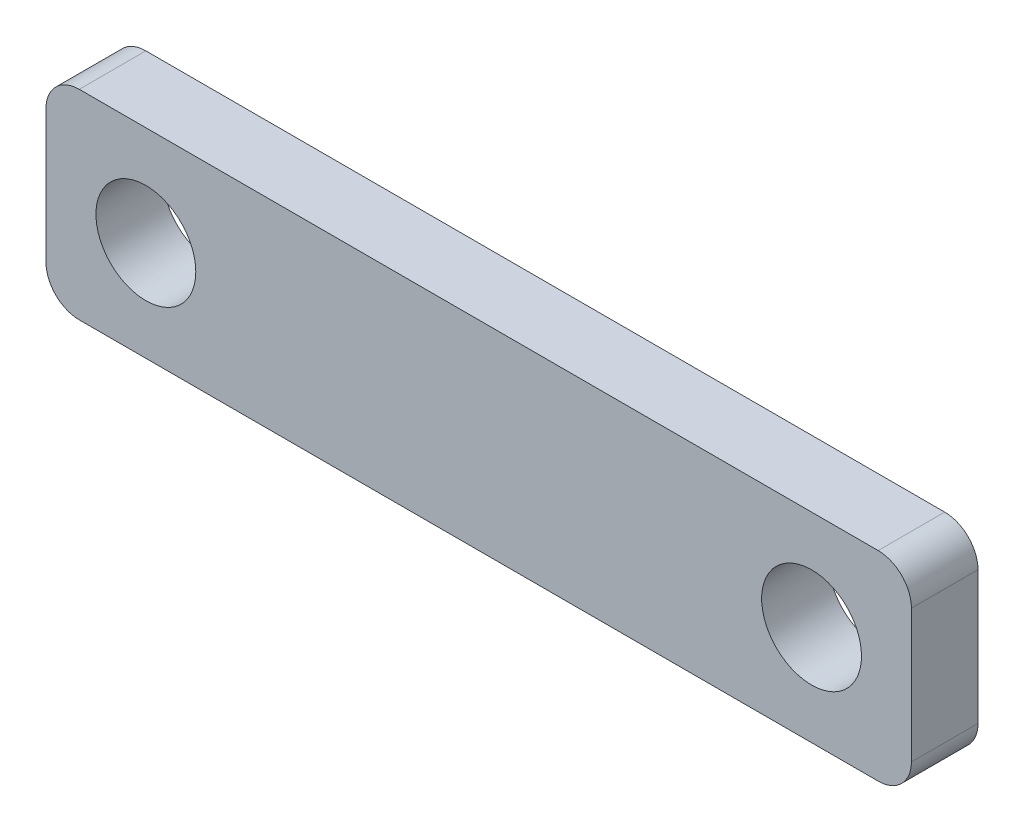
SolidWorks part; units mm, degrees
ref_plane "Plan de face" through (0, 0, 0) normal (0, 0, 1) x (1, 0, 0)
ref_plane "Plan de dessus" through (0, 0, 0) normal (0, 1, 0) x (1, 0, 0)
ref_plane "Plan de droite" through (0, 0, 0) normal (1, 0, 0) x (0, 0, -1)
sketch "Esquisse1" plane through (0, 0, 0) normal (0, 0, 1) x (1, 0, 0)
  line L1 (-13, -3) -> (13, -3)
  line L2 (-13, -3) -> (-13, 3)
  line L3 (-13, 3) -> (13, 3)
  line L4 (13, -3) -> (13, 3)
  line L5 (-13, -3) -> (13, 3) construction
  line L6 (-13, 3) -> (13, -3) construction
  circle A0 centre (10, 0) radius 1.5
  circle A1 centre (-10, 0) radius 1.5
  point P0 (0, 0)
  dimension "D3" = 3
  dimension "D1" = 26
  dimension "D2" = 6
  dimension "D4" = 3
  dimension "D5" = 3
extrude "Boss.-Extru.1" add sketch "Esquisse1" along normal blind 2
fillet "Congé1" radius 1 4 edges at (-13, -3, 1) (13, -3, 1) (13, 3, 1) (-13, 3, 1)
